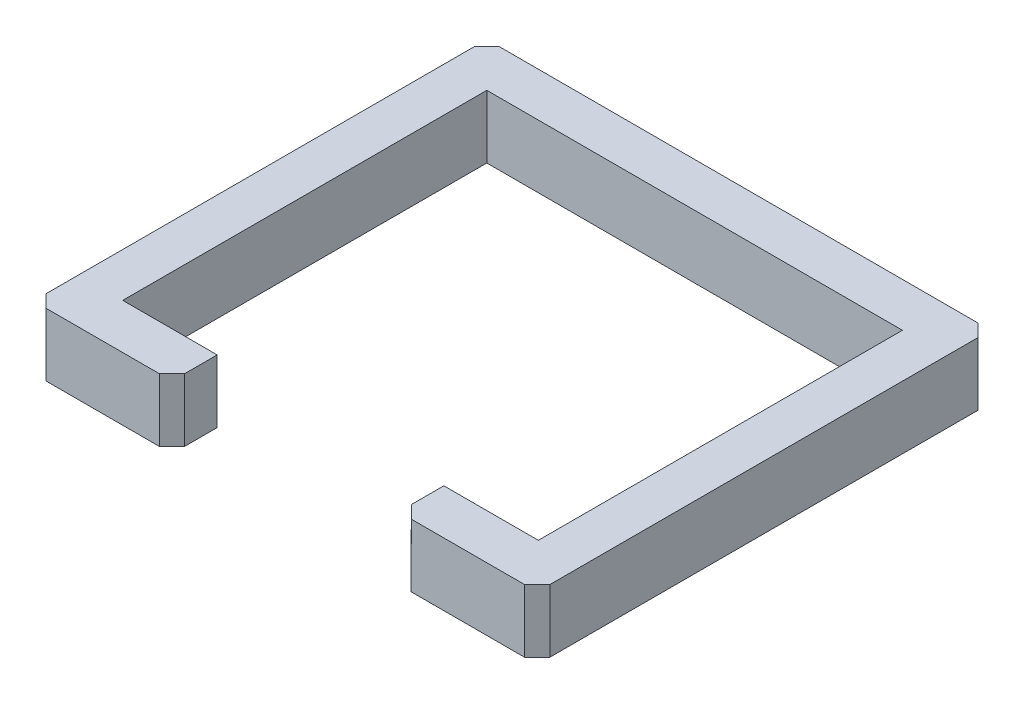
SolidWorks part; units mm, degrees
material "Polyurethane Foam Flexible"
ref_plane "Front Plane" through (0, 0, 0) normal (0, 0, 1) x (1, 0, 0)
ref_plane "Top Plane" through (0, 0, 0) normal (0, 1, 0) x (1, 0, 0)
ref_plane "Right Plane" through (0, 0, 0) normal (1, 0, 0) x (0, 0, -1)
sketch "Sketch1" plane through (0, 57.8438, 0) normal (0, -1, 0.0004) x (-1, 0, 0)
  line L0 (489.4342, 347.5456) -> (489.4342, -386.7871)
  line L1 (489.4342, -386.7871) -> (298.9342, -386.7871)
  line L2 (298.9342, -386.7871) -> (298.9342, -452.5544)
  line L3 (-158.2658, -452.5544) -> (-158.2658, -386.7871)
  line L4 (-158.2658, -386.7871) -> (-348.7658, -386.7871)
  line L5 (-348.7658, -386.7871) -> (-348.7658, 347.5456)
  line L6 (-348.7658, 347.5456) -> (489.4342, 347.5456)
  line L7 (324.3342, -477.9545) -> (552.9342, -477.9545)
  line L8 (578.3342, -452.5544) -> (578.3342, 411.0456)
  line L9 (552.9342, 436.4456) -> (-412.2658, 436.4456)
  line L10 (-437.6658, 411.0456) -> (-437.6658, -452.5544)
  line L11 (-412.2658, -477.9545) -> (-183.6658, -477.9545)
  line L12 (-412.2658, -477.9545) -> (-183.6658, -477.9545)
  line L13 (-437.6658, 411.0456) -> (-437.6658, -452.5544)
  line L14 (552.9342, 436.4456) -> (-412.2658, 436.4456)
  line L15 (578.3342, -452.5544) -> (578.3342, 411.0456)
  line L16 (324.3342, -477.9545) -> (552.9342, -477.9545)
  line L17 (-348.7658, 347.5456) -> (489.4342, 347.5456)
  line L18 (-348.7658, -386.7871) -> (-348.7658, 347.5456)
  line L19 (-158.2658, -386.7871) -> (-348.7658, -386.7871)
  line L20 (-158.2658, -452.5544) -> (-158.2658, -386.7871)
  line L21 (298.9342, -386.7871) -> (298.9342, -452.5544)
  line L22 (489.4342, -386.7871) -> (298.9342, -386.7871)
  line L23 (489.4342, 347.5456) -> (489.4342, -386.7871)
  line L24 (578.3342, -452.5544) -> (552.9342, -477.9545)
  line L25 (324.3342, -477.9545) -> (298.9342, -452.5544)
  line L26 (-158.2658, -452.5544) -> (-183.6658, -477.9545)
  line L27 (-412.2658, -477.9545) -> (-437.6658, -452.5544)
  line L28 (-437.6658, 411.0456) -> (-412.2658, 436.4456)
  line L29 (578.3342, 411.0456) -> (552.9342, 436.4456)
  arc A0 (-437.6658, -452.5544) -> (-412.2658, -477.9545) centre (-412.2658, -452.5544) ccw
  arc A1 (552.9342, -477.9545) -> (578.3342, -452.5544) centre (552.9342, -452.5544) ccw
  arc A2 (298.9342, -452.5544) -> (324.3342, -477.9545) centre (324.3342, -452.5544) ccw
  arc A3 (-183.6658, -477.9545) -> (-158.2658, -452.5544) centre (-183.6658, -452.5544) ccw
  arc A4 (-412.2658, 436.4456) -> (-437.6658, 411.0456) centre (-412.2658, 411.0456) ccw
  arc A5 (578.3342, 411.0456) -> (552.9342, 436.4456) centre (552.9342, 411.0456) ccw
  arc A6 (578.3342, 411.0456) -> (552.9342, 436.4456) centre (552.9342, 411.0456) ccw
  arc A7 (-412.2658, 436.4456) -> (-437.6658, 411.0456) centre (-412.2658, 411.0456) ccw
  arc A8 (-183.6658, -477.9545) -> (-158.2658, -452.5544) centre (-183.6658, -452.5544) ccw
  arc A9 (298.9342, -452.5544) -> (324.3342, -477.9545) centre (324.3342, -452.5544) ccw
  arc A10 (552.9342, -477.9545) -> (578.3342, -452.5544) centre (552.9342, -452.5544) ccw
  arc A11 (-437.6658, -452.5544) -> (-412.2658, -477.9545) centre (-412.2658, -452.5544) ccw
extrude "Boss-Extrude1" add sketch "Sketch1" along normal mid plane 127 contours L21 A9 L25 L16 L24 L15 L29 L14 L28 L13 L27 L12 L26 L20 L19 L18 L17 L23 L22
